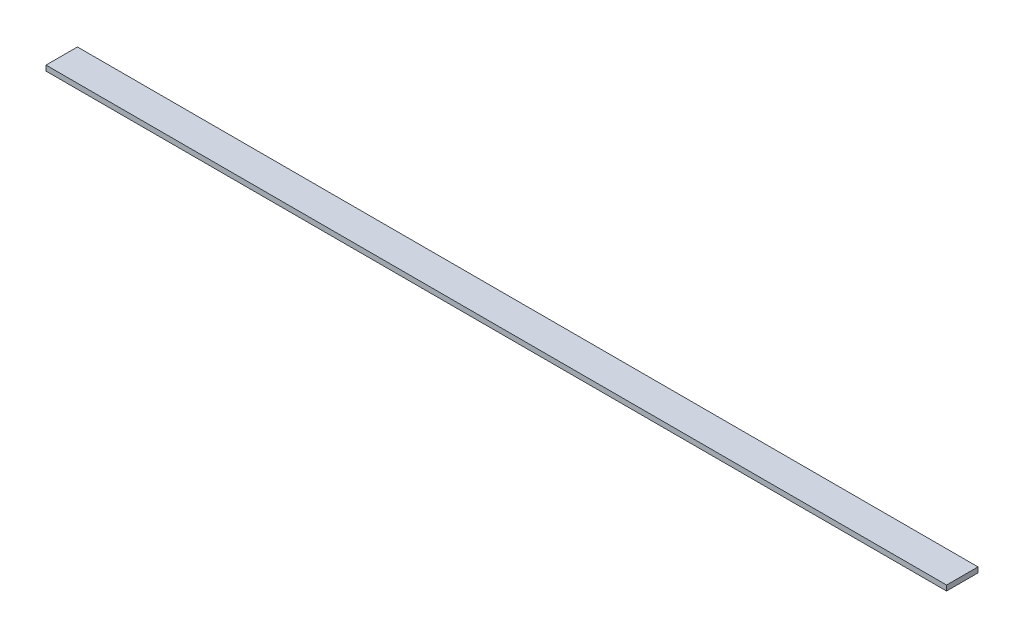
SolidWorks part; units mm, degrees
ref_plane "Front Plane" through (0, 0, 0) normal (0, 0, 1) x (1, 0, 0)
ref_plane "Top Plane" through (0, 0, 0) normal (0, 1, 0) x (1, 0, 0)
ref_plane "Right Plane" through (0, 0, 0) normal (1, 0, 0) x (0, 0, -1)
sketch "Sketch1" plane through (0, 0, 0) normal (0, 1, 0) x (1, 0, 0)
  line L1 (-136.525, 4.7625) -> (136.525, 4.7625)
  line L2 (-136.525, 4.7625) -> (-136.525, -4.7625)
  line L3 (-136.525, -4.7625) -> (136.525, -4.7625)
  line L4 (136.525, 4.7625) -> (136.525, -4.7625)
  line L5 (-136.525, 4.7625) -> (136.525, -4.7625) construction
  line L6 (-136.525, -4.7625) -> (136.525, 4.7625) construction
  point P0 (0, 0)
  dimension "D1" = 273.05
  dimension "D2" = 9.525
extrude "Boss-Extrude1" add sketch "Sketch1" along normal blind 1.5875
